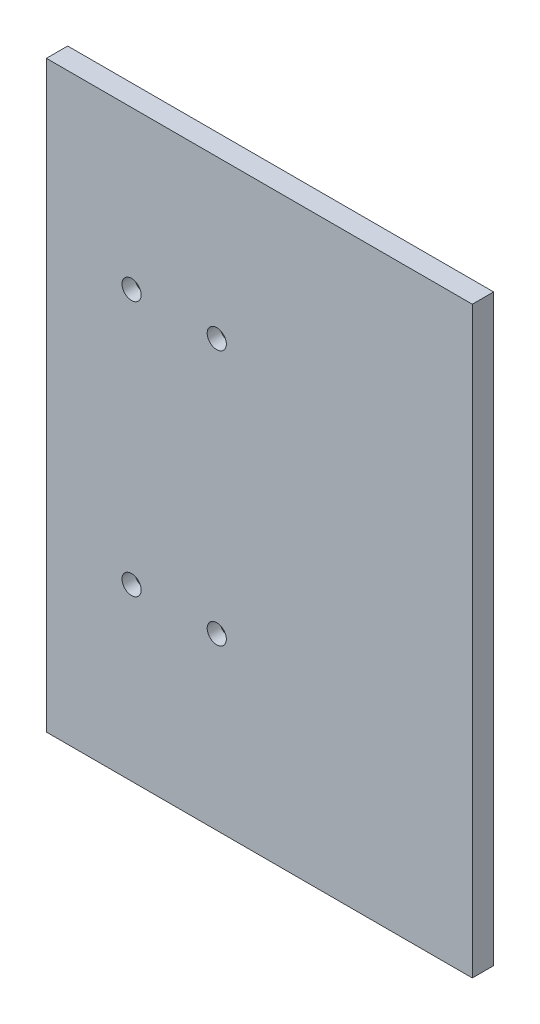
SolidWorks part; units mm, degrees
material "ABS"
ref_plane "Front Plane" through (0, 0, 0) normal (0, 0, 1) x (1, 0, 0)
ref_plane "Top Plane" through (0, 0, 0) normal (0, 1, 0) x (1, 0, 0)
ref_plane "Right Plane" through (0, 0, 0) normal (1, 0, 0) x (0, 0, -1)
sketch "Sketch1" plane through (0, 0, 0) normal (0, 0, 1) x (1, 0, 0)
  line L0 (0, 173.99) -> (63.5, 173.99)
  line L1 (0, 173.99) -> (-63.5, 173.99)
  line L7 (-63.5, 173.99) -> (-63.5, 0)
  line L8 (63.5, 173.99) -> (63.5, 0)
  line L9 (63.5, 0) -> (-63.5, 0)
extrude "Boss-Extrude1" add sketch "Sketch1" along normal blind 6.35
sketch "Sketch2" plane through (0, 0, 0) normal (0, 0, -1) x (-1, 0, 0)
  line L0 (-43.0645, 133.5103) -> (-3.6945, 133.5103)
  line L1 (-43.0645, 51.4703) -> (-3.6945, 51.4703)
  line L2 (-43.0645, 51.4703) -> (-43.0645, 133.5103)
  circle A0 centre (-43.0645, 133.5103) radius 2.8575
  circle A1 centre (-3.6945, 133.5103) radius 2.8575
  circle A2 centre (-43.0645, 51.4703) radius 2.8575
  circle A3 centre (-3.6945, 51.4703) radius 2.8575
  dimension "D1" = 5.715
sketch "Sketch3" plane through (0, 0, 6.35) normal (0, 0, 1) x (1, 0, 0)
  circle A0 centre (-38.1, 127) radius 2.8575
  circle A1 centre (-12.7, 127) radius 2.8575
  circle A2 centre (-38.1, 50.8) radius 2.8575
  circle A3 centre (-12.7, 50.8) radius 2.8575
  dimension "D1" = 5.715
extrude "Cut-Extrude1" cut sketch "Sketch3" against normal blind 3.81 contours A0 | A1 | A3 | A2
extrude "Cut-Extrude2" cut sketch "Sketch2" against normal blind 3.81 contours A0 | A1 | A3 | A2
